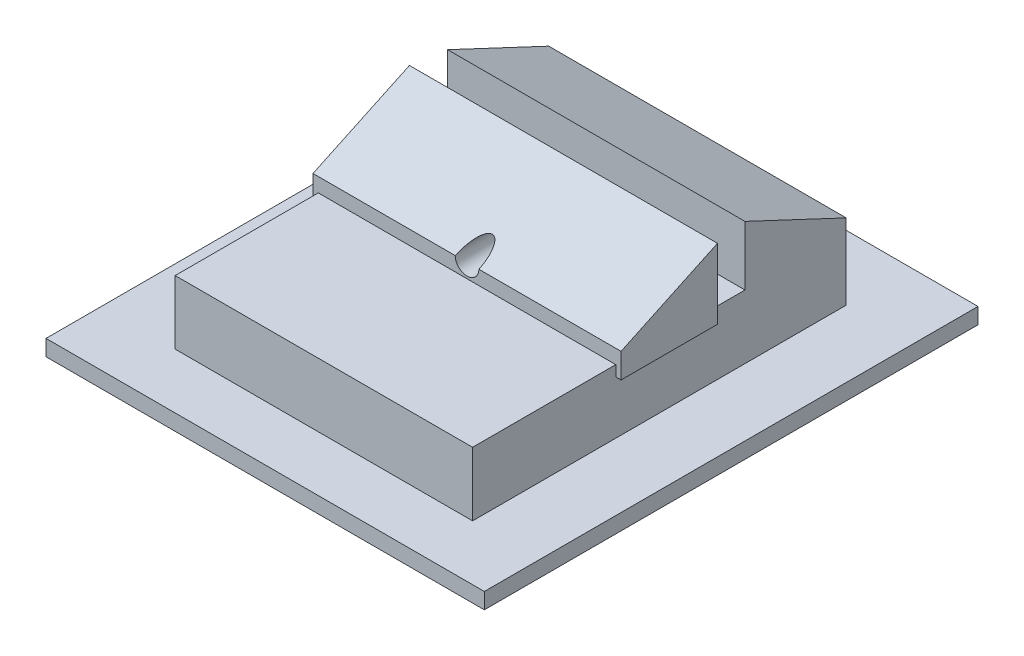
SolidWorks part; units mm, degrees
ref_plane "Front Plane" through (0, 0, 0) normal (0, 0, 1) x (1, 0, 0)
ref_plane "Top Plane" through (0, 0, 0) normal (0, 1, 0) x (1, 0, 0)
ref_plane "Right Plane" through (0, 0, 0) normal (1, 0, 0) x (0, 0, -1)
sketch "Sketch1" plane through (0, 0, 0) normal (1, 0, 0) x (0, 0, -1)
  line L0 (-33.5857, 72.8507) -> (-33.5857, 73.9677)
  line L1 (-68.7551, 72.8507) -> (-33.5857, 72.8507)
  line L2 (-68.7551, 72.8507) -> (-68.7551, 66.8507)
  line L3 (-68.7551, 66.8507) -> (-33.5857, 66.8507)
  line L4 (-33.5857, 72.8507) -> (-33.5857, 66.8507)
  line L5 (-43.1121, 72.8507) -> (-43.1121, 78.4445)
  line L6 (-43.1121, 78.4445) -> (-33.5857, 73.9677)
  line L8 (-55.2786, 72.8507) -> (-55.2786, 74.1848)
  line L9 (-46.2, 78.4511) -> (-55.2786, 74.1848)
  line L10 (-46.2, 72.8507) -> (-46.2, 78.4511)
extrude "Boss-Extrude1" add sketch "Sketch1" along normal blind 25 contours L1 L10 L9 L8 | L4 L1 L2 L3 | L6 L5 L1 L0
sketch "Sketch2" plane through (25, 0, 0) normal (1, 0, 0) x (0, 0, -1)
  line L1 (-68.7551, 72.8507) -> (-33.5857, 72.8507)
  line L2 (-68.7551, 72.8507) -> (-68.7551, 66.8507)
  line L3 (-68.7551, 66.8507) -> (-33.5857, 66.8507)
  line L4 (-33.5857, 72.8507) -> (-33.5857, 66.8507)
extrude "Boss-Extrude2" add sketch "Sketch2" along normal blind 1.5
sketch "Sketch3" plane through (0, 0, 0) normal (-1, 0, 0) x (0, 0, 1)
  line L1 (33.5857, 66.8507) -> (68.7551, 66.8507)
  line L2 (33.5857, 66.8507) -> (33.5857, 72.8507)
  line L3 (33.5857, 72.8507) -> (68.7551, 72.8507)
  line L4 (68.7551, 66.8507) -> (68.7551, 72.8507)
extrude "Boss-Extrude3" add sketch "Sketch3" along normal blind 1.5
sketch "Sketch4" plane through (0, 66.8507, 0) normal (0, -1, 0) x (1, 0, 0)
  line L1 (-8.4565, 73.9567) -> (32.806, 73.9567)
  line L2 (-8.4565, 73.9567) -> (-8.4565, 27.4836)
  line L3 (-8.4565, 27.4836) -> (32.806, 27.4836)
  line L4 (32.806, 73.9567) -> (32.806, 27.4836)
extrude "Boss-Extrude4" add sketch "Sketch4" along normal blind 1.5
sketch "Sketch6" plane through (25, 0, 0) normal (1, 0, 0) x (0, 0, -1)
  line L0 (-55.2786, 72.8507) -> (-55.2786, 74.1848)
  line L1 (-55.2786, 74.1848) -> (-46.2, 78.4511)
  line L2 (-46.2, 78.4511) -> (-46.2, 72.8507)
  line L3 (-46.2, 72.8507) -> (-55.2786, 72.8507)
extrude "Boss-Extrude5" add sketch "Sketch6" along normal blind 2
sketch "Sketch7" plane through (0, 0, 0) normal (-1, 0, 0) x (0, 0, 1)
  line L4 (46.2, 72.8507) -> (55.2786, 72.8507)
  line L5 (55.2786, 72.8507) -> (55.2786, 74.1848)
  line L6 (55.2786, 74.1848) -> (46.2, 78.4511)
  line L7 (46.2, 78.4511) -> (46.2, 72.8507)
  line L8 (46.2, 72.8507) -> (55.2786, 72.8507)
  line L9 (55.2786, 72.8507) -> (55.2786, 74.1848)
  line L10 (55.2786, 74.1848) -> (46.2, 78.4511)
  line L11 (46.2, 78.4511) -> (46.2, 72.8507)
  dimension "D1" = 0
extrude "Boss-Extrude6" add sketch "Sketch7" along normal blind 2
sketch "Sketch8" plane through (26.5, 0, 0) normal (1, 0, 0) x (0, 0, -1)
  line L0 (-55.2786, 72.8507) -> (-55.2786, 71.8507)
  line L1 (-55.2786, 71.8507) -> (-46.2, 71.8507)
  line L2 (-46.2, 71.8507) -> (-46.2, 72.8507)
  line L3 (-46.2, 72.8507) -> (-55.2786, 72.8507)
extrude "Boss-Extrude7" add sketch "Sketch8" along normal blind 0.5
sketch "Sketch9" plane through (-1.5, 0, 0) normal (-1, 0, 0) x (0, 0, 1)
  line L0 (46.2, 72.8507) -> (46.2, 71.8507)
  line L1 (46.2, 71.8507) -> (55.2786, 71.8507)
  line L2 (55.2786, 71.8507) -> (55.2786, 72.8507)
  line L3 (55.2786, 72.8507) -> (46.2, 72.8507)
  line L4 (46.2, 72.8507) -> (47.5239, 72.8415)
extrude "Boss-Extrude8" add sketch "Sketch9" along normal blind 0.5
sketch "Sketch10" plane through (25, 0, 0) normal (1, 0, 0) x (0, 0, -1)
  line L4 (-43.1121, 72.8507) -> (-33.5857, 72.8507)
  line L5 (-33.5857, 72.8507) -> (-33.5857, 73.9677)
  line L6 (-33.5857, 73.9677) -> (-43.1121, 78.4445)
  line L7 (-43.1121, 78.4445) -> (-43.1121, 72.8507)
  line L8 (-43.1121, 72.8507) -> (-33.5857, 72.8507)
  line L9 (-33.5857, 72.8507) -> (-33.5857, 73.9677)
  line L10 (-33.5857, 73.9677) -> (-43.1121, 78.4445)
  line L11 (-43.1121, 78.4445) -> (-43.1121, 72.8507)
  dimension "D1" = 0
extrude "Boss-Extrude9" add sketch "Sketch10" along normal blind 1.5
sketch "Sketch11" plane through (0, 0, 0) normal (-1, 0, 0) x (0, 0, 1)
  line L4 (33.5857, 72.8507) -> (43.1121, 72.8507)
  line L5 (43.1121, 72.8507) -> (43.1121, 78.4445)
  line L6 (43.1121, 78.4445) -> (33.5857, 73.9677)
  line L7 (33.5857, 73.9677) -> (33.5857, 72.8507)
  line L8 (33.5857, 72.8507) -> (43.1121, 72.8507)
  line L9 (43.1121, 72.8507) -> (43.1121, 78.4445)
  line L10 (43.1121, 78.4445) -> (33.5857, 73.9677)
  line L11 (33.5857, 73.9677) -> (33.5857, 72.8507)
  dimension "D1" = 0
extrude "Boss-Extrude10" add sketch "Sketch11" along normal blind 1.5
sketch "Sketch13" plane through (0, 0, 55.2786) normal (0, 0, 1) x (1, 0, 0)
  line L0 (27, 74.1848) -> (-2, 74.1848) construction
  circle A0 centre (12.5, 74.1848) radius 1.1144
extrude "Cut-Extrude1" cut sketch "Sketch13" against normal blind 10
